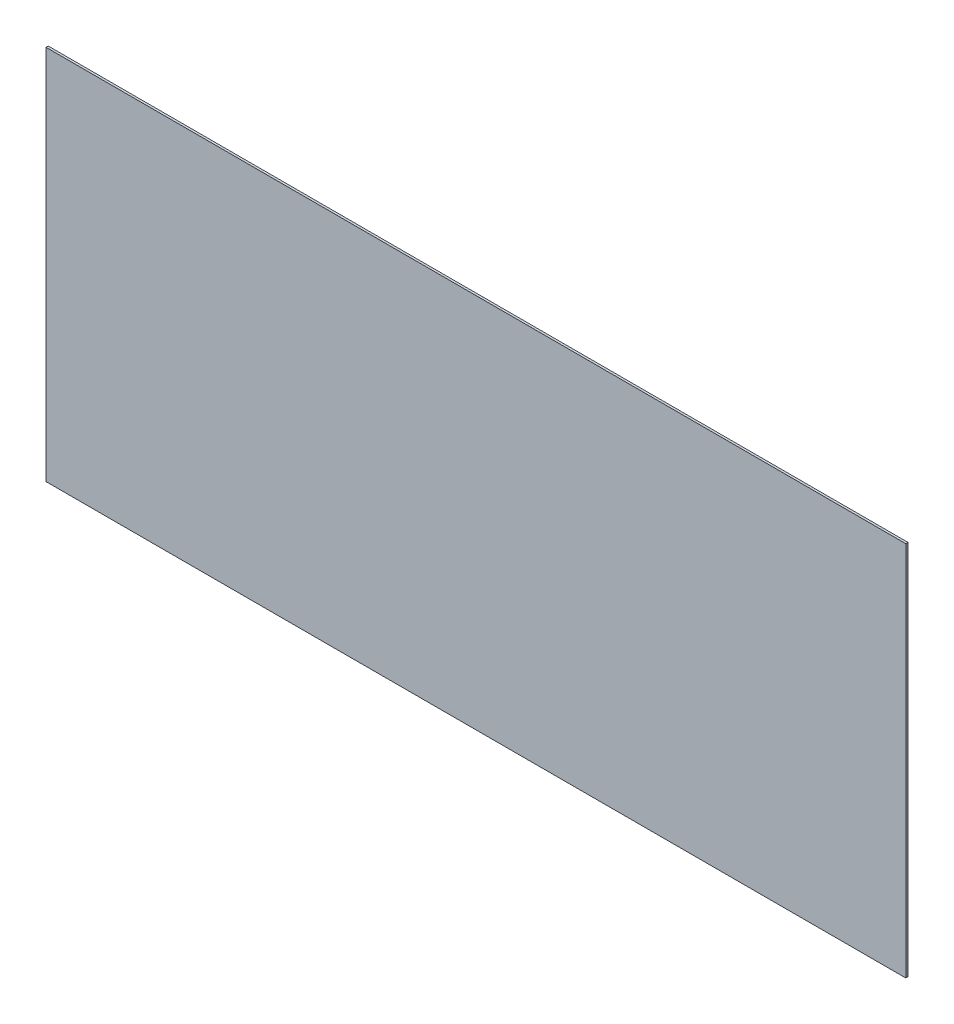
SolidWorks part; units mm, degrees
material "Pine"
ref_plane "Front Plane" through (0, 0, 0) normal (0, 0, 1) x (1, 0, 0)
ref_plane "Top Plane" through (0, 0, 0) normal (0, 1, 0) x (1, 0, 0)
ref_plane "Right Plane" through (0, 0, 0) normal (1, 0, 0) x (0, 0, -1)
sketch "Sketch1" plane through (0, 0, 0) normal (0, 0, 1) x (1, 0, 0)
  line L1 (0, 0) -> (1219.2, 0)
  line L2 (0, 0) -> (0, 533.4)
  line L3 (0, 533.4) -> (1219.2, 533.4)
  line L4 (1219.2, 0) -> (1219.2, 533.4)
  dimension "D1" = 533.4
  dimension "D2" = 1219.2
extrude "Boss-Extrude1" add sketch "Sketch1" along normal blind 3.175
